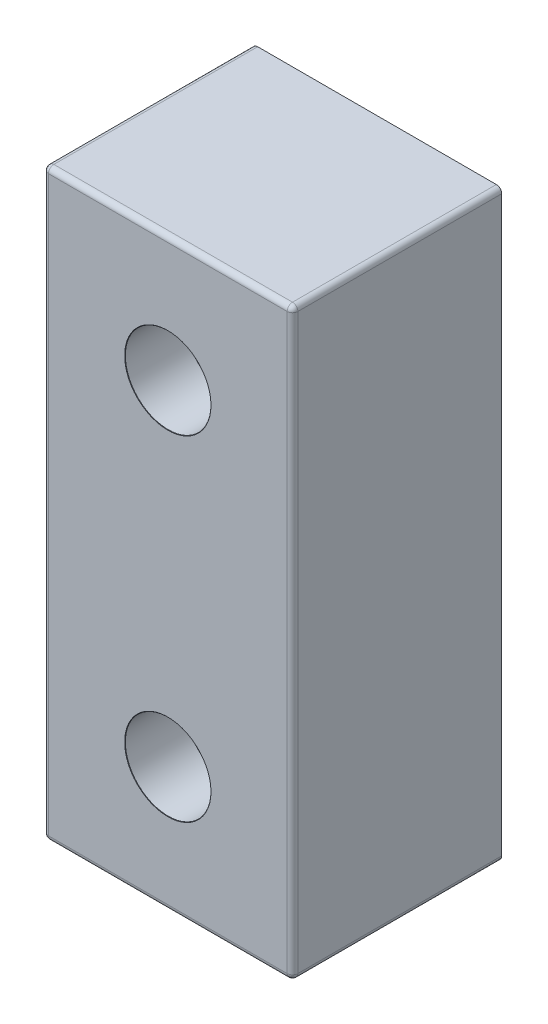
SolidWorks part; units mm, degrees
ref_plane "Front Plane" through (0, 0, 0) normal (0, 0, 1) x (1, 0, 0)
ref_plane "Top Plane" through (0, 0, 0) normal (0, 1, 0) x (1, 0, 0)
ref_plane "Right Plane" through (0, 0, 0) normal (1, 0, 0) x (0, 0, -1)
sketch "Sketch1" plane through (0, 0, 0) normal (0, 0, 1) x (1, 0, 0)
  line L0 (-3.175, -3.175) -> (-3.175, 47.498)
  line L1 (0, 0) -> (18.923, 0)
  line L2 (0, 0) -> (0, 44.323)
  line L3 (0, 44.323) -> (18.923, 44.323)
  line L4 (18.923, 0) -> (18.923, 44.323)
  line L5 (-3.175, 47.498) -> (22.098, 47.498)
  line L6 (22.098, -3.175) -> (22.098, 47.498)
  line L7 (-3.175, -3.175) -> (22.098, -3.175)
  line L8 (18.923, 22.1615) -> (0, 22.1615) construction
  line L9 (9.4615, 44.323) -> (9.4615, 22.1615) construction
  line L10 (9.4615, 22.1615) -> (9.4615, 0) construction
  circle A0 centre (9.4615, 34.8615) radius 1.5875
  circle A1 centre (9.4615, 9.4615) radius 1.5875
  dimension "D5" = 3.175
  dimension "D1" = 44.323
  dimension "D2" = 18.923
  dimension "D6" = 12.7
  dimension "D7" = 12.7
  dimension "D3" = 3.175
extrude "Boss-Extrude1" add sketch "Sketch1" along normal blind 15.875 contours L1 L4 L3 L2 A1 A0
fillet "Fillet1" radius 0.4064 10 edges at (0, 0, 7.9375) (18.923, 0, 7.9375) (0, 44.323, 7.9375) (18.923, 44.323, 7.9375) (0, 22.1615, 15.875) (9.4615, 44.323, 15.875) (18.923, 22.1615, 15.875) (9.4615, 0, 15.875) (11.049, 34.8615, 15.875) (11.049, 9.4615, 15.875)
hole_wizard "CBORE for M3 SHCS1" positions "3DSketch1" profile "Sketch2" counterbore size "M3" standard "ANSI Metric"
sketch3d "3DSketch1"
  line L0 (9.4615, 9.4615, 15.4686) -> (9.4615, 9.4615, 0) construction
  line L1 (9.4615, 34.8615, 15.4686) -> (9.4615, 34.8615, 0) construction
  circle A0 centre (9.4615, 34.8615, 15.875) radius 1.5875 construction
  point P0 (9.4615, 9.4615, 15.875)
  point P4 (10.8894, 34.1678, 15.875)
  point P8 (9.4615, 34.8615, 17.4625)
  point P9 (9.4615, 34.8615, 15.875)
sketch "Sketch2" plane through (9.4615, 9.4615, 15.875) normal (1, 0, 0) x (0, -1, 0)
  line L0 (0, 0) -> (0, 15.875)
  line L1 (0, 15.875) -> (1.6, 15.875)
  line L3 (1.6, 15.875) -> (1.6, 4.5875)
  line L4 (3.25, 4.5875) -> (1.6, 4.5875)
  line L5 (3.25, 4.5875) -> (3.25, 0.025)
  line L6 (3.25, 0.025) -> (3.275, 0)
  line L7 (3.275, 0) -> (0, 0)
  line L8 (-3.25, 0.025) -> (-3.275, 0) construction
  line L11 (0, -6.35) -> (0, 107.95) construction
  dimension "Thru Hole Dia." = 3.2
  dimension "Thru Hole Depth" = 15.875
  dimension "C'Bore Dia." = 6.5
  dimension "C'Bore Depth" = 4.5875
  dimension "Near C'Sink Dia." = 6.55
  dimension "Near C'Sink Angle" = 90
equation "\"D6@Sketch1\"=\"D7@Sketch1\""
